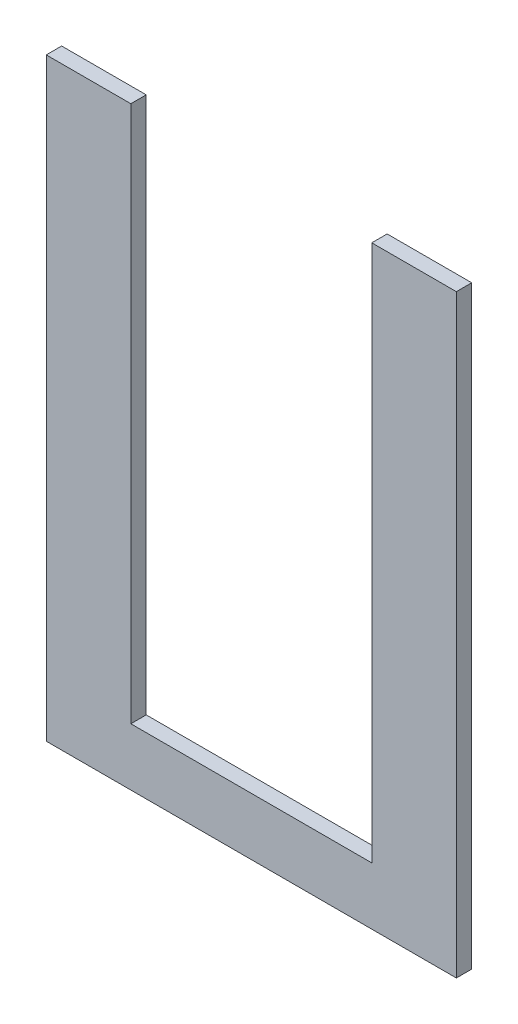
SolidWorks part; units mm, degrees
ref_plane "Front Plane" through (0, 0, 0) normal (0, 0, 1) x (1, 0, 0)
ref_plane "Top Plane" through (0, 0, 0) normal (0, 1, 0) x (1, 0, 0)
ref_plane "Right Plane" through (0, 0, 0) normal (1, 0, 0) x (0, 0, -1)
sketch "Sketch1" plane through (0, 0, 0) normal (0, 0, 1) x (1, 0, 0)
  line L0 (16.5, 11.2) -> (63.5, 11.2) construction
  line L1 (0, 0) -> (80, 0)
  line L2 (0, 0) -> (0, 115.957)
  line L3 (0, 115.957) -> (80, 115.957) construction
  line L4 (80, 0) -> (80, 115.957)
  line L5 (16.5, 115.957) -> (16.5, 11.2) construction
  line L6 (63.5, 11.2) -> (63.5, 115.957) construction
  line L7 (16.5, 11.2) -> (63.5, 11.2)
  line L8 (16.5, 115.957) -> (16.5, 11.2)
  line L9 (63.5, 11.2) -> (63.5, 115.957)
  line L10 (40, 115.957) -> (40, 0) construction
  line L11 (0, 115.957) -> (16.5, 115.957)
  line L12 (63.5, 115.957) -> (80, 115.957)
sketch "Sketch2" plane through (0, 0, 0) normal (0, 1, 0) x (1, 0, 0)
  line L1 (0, 0) -> (80, 0)
  line L2 (0, 0) -> (0, 3)
  line L3 (0, 3) -> (80, 3)
  line L4 (80, 0) -> (80, 3)
extrude "Boss-Extrude1" add sketch "Sketch1" against normal up to vertex (3 mm away) up to point (80, 0, -3)
